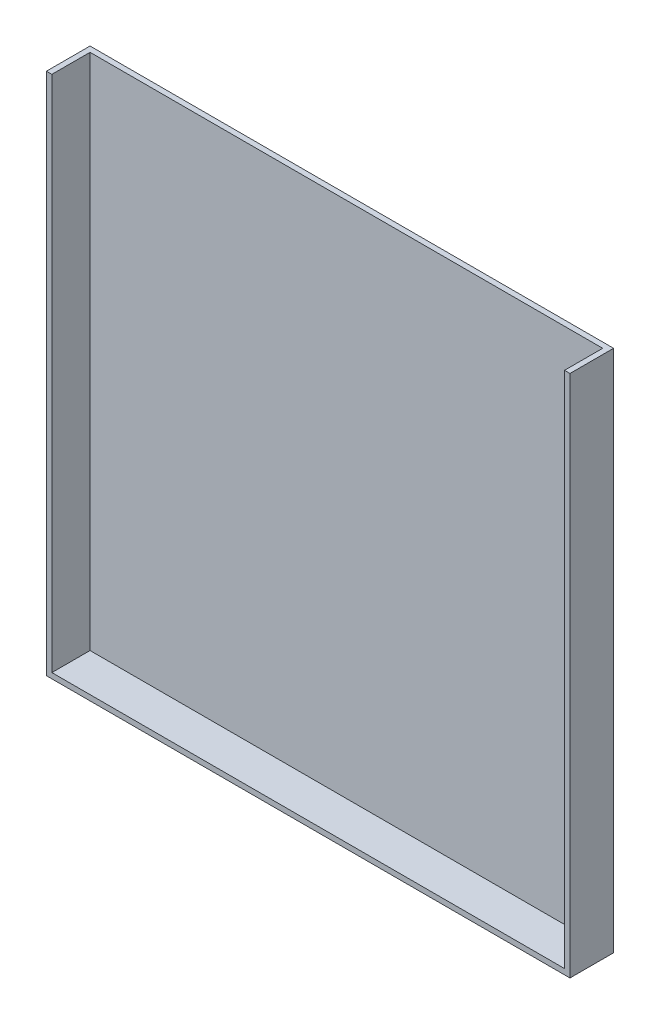
SolidWorks part; units mm, degrees
ref_plane "Front Plane" through (0, 0, 0) normal (0, 0, 1) x (1, 0, 0)
ref_plane "Top Plane" through (0, 0, 0) normal (0, 1, 0) x (1, 0, 0)
ref_plane "Right Plane" through (0, 0, 0) normal (1, 0, 0) x (0, 0, -1)
sketch "Sketch2" plane through (0, 0, 0) normal (0, 0, 1) x (1, 0, 0)
  line L1 (0, 0) -> (304.8, 0)
  line L2 (0, 0) -> (0, 304.8)
  line L3 (0, 304.8) -> (304.8, 304.8)
  line L4 (304.8, 0) -> (304.8, 304.8)
  dimension "D1" = 304.8
  dimension "D2" = 304.8
extrude "Boss-Extrude1" add sketch "Sketch2" along normal blind 25.4
shell "Shell1" thickness 3.175
